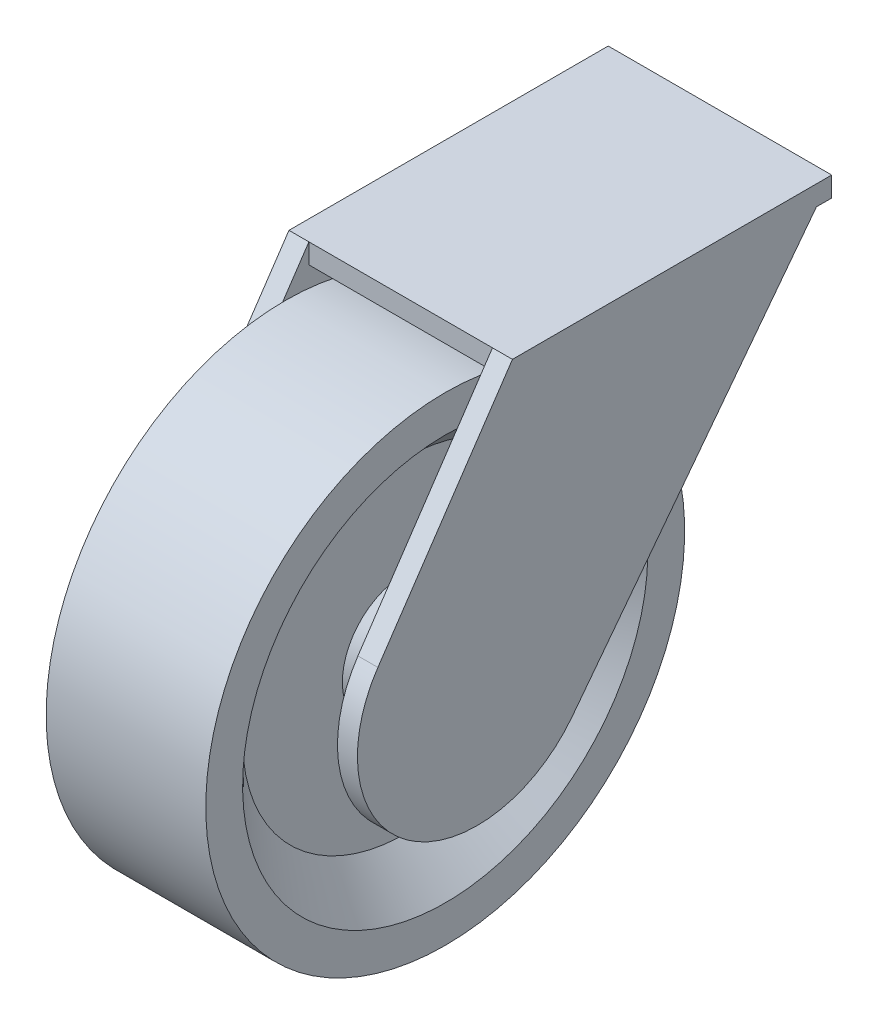
SolidWorks part; units mm, degrees
ref_plane "Front Plane" through (0, 0, 0) normal (0, 0, 1) x (1, 0, 0)
ref_plane "Top Plane" through (0, 0, 0) normal (0, 1, 0) x (1, 0, 0)
ref_plane "Right Plane" through (0, 0, 0) normal (1, 0, 0) x (0, 0, -1)
sketch "Sketch1" plane through (0, 0, 0) normal (0, 0, 1) x (1, 0, 0)
  line L0 (-40, 60) -> (0, 60)
  line L1 (0, 60) -> (0, 50.7735)
  line L2 (0, 50.7735) -> (-10, 40.7735)
  line L3 (-10, 40.7735) -> (-10, 15.7735)
  line L4 (-10, 15.7735) -> (0, 10)
  line L5 (0, 10) -> (0, 0)
  line L6 (0, 0) -> (-40, 0)
  line L8 (-20, 60) -> (-20, -29.9521) construction
  line L9 (-40, 10) -> (-40, 0)
  line L10 (-30, 15.7735) -> (-40, 10)
  line L11 (-30, 40.7735) -> (-30, 15.7735)
  line L12 (-40, 50.7735) -> (-30, 40.7735)
  line L13 (-40, 60) -> (-40, 50.7735)
  dimension "D1" = 60
  dimension "D2" = 40
  dimension "D4" = 135
  dimension "D5" = 120
  dimension "D6" = 25
  dimension "D7" = 10
revolve "Revolve1" add sketch "Sketch1" angle 360 about L6
sketch "Sketch3" plane through (0, 0, 0) normal (1, 0, 0) x (0, 0, -1)
  circle A0 centre (0, 0) radius 7.5
  dimension "D1" = 15
extrude "Boss-Extrude1" add sketch "Sketch3" along normal blind 8
sketch "Sketch4" plane through (8, 0, 0) normal (1, 0, 0) x (0, 0, -1)
  line L0 (8.8458, 66.7734) -> (88.8458, 66.7734)
  line L1 (88.8458, 66.7734) -> (23.8284, -18.2266)
  line L2 (-24.8727, 16.7734) -> (8.8458, 66.7734)
  arc A0 (23.8284, -18.2266) -> (-24.8727, 16.7734) centre (0, 0) cw
  circle A1 centre (0, 0) radius 7.5 construction
  dimension "D4" = 30
  dimension "D1" = 80
  dimension "D2" = 85
  dimension "D3" = 50
extrude "Boss-Extrude2" add sketch "Sketch4" against normal blind 5
ref_plane "Plane1" through (-20, 0, 0) normal (1, 0, 0) x (0, 0, -1)
mirror "Mirror1" about plane through (-20, 0, 0) normal (1, 0, 0) of "Boss-Extrude2", "Boss-Extrude1"
sketch "Sketch5" plane through (0, 66.7734, 0) normal (0, 1, 0) x (1, 0, 0)
  line L1 (-48, 88.8458) -> (8, 88.8458)
  line L2 (-48, 88.8458) -> (-48, 8.8458)
  line L3 (-48, 8.8458) -> (8, 8.8458)
  line L4 (8, 88.8458) -> (8, 8.8458)
extrude "Boss-Extrude3" add sketch "Sketch5" against normal blind 5
scale "Scale1" scale about centroid uniform scaling yes scale factor 0.5
